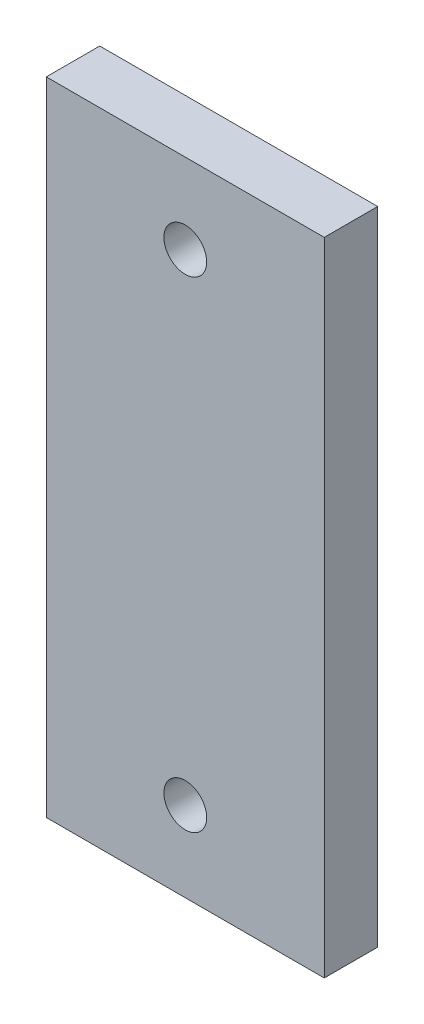
SolidWorks part; units mm, degrees
ref_plane "前视基准面" through (0, 0, 0) normal (0, 0, 1) x (1, 0, 0)
ref_plane "上视基准面" through (0, 0, 0) normal (0, 1, 0) x (1, 0, 0)
ref_plane "右视基准面" through (0, 0, 0) normal (1, 0, 0) x (0, 0, -1)
sketch "草图1" plane through (0, 0, 0) normal (0, 0, 1) x (1, 0, 0)
  line L0 (-37.4967, 31.7663) -> (-11.4967, 31.7663)
  line L1 (-11.4967, 31.7663) -> (-11.4967, -28.2337)
  line L2 (-11.4967, -28.2337) -> (-37.4967, -28.2337)
  line L3 (-37.4967, -28.2337) -> (-37.4967, 31.7663)
  line L4 (-24.4967, 31.7663) -> (-24.4967, 24.2663) construction
  line L5 (-37.4967, 1.7663) -> (-11.4967, 1.7663) construction
  circle A0 centre (-24.4967, 24.2663) radius 2
  circle A1 centre (-24.4967, -20.7337) radius 2
  dimension "D4" = 4
  dimension "D1" = 26
  dimension "D2" = 60
  dimension "D3" = 7.5
extrude "凸台-拉伸1" add sketch "草图1" along normal blind 5
